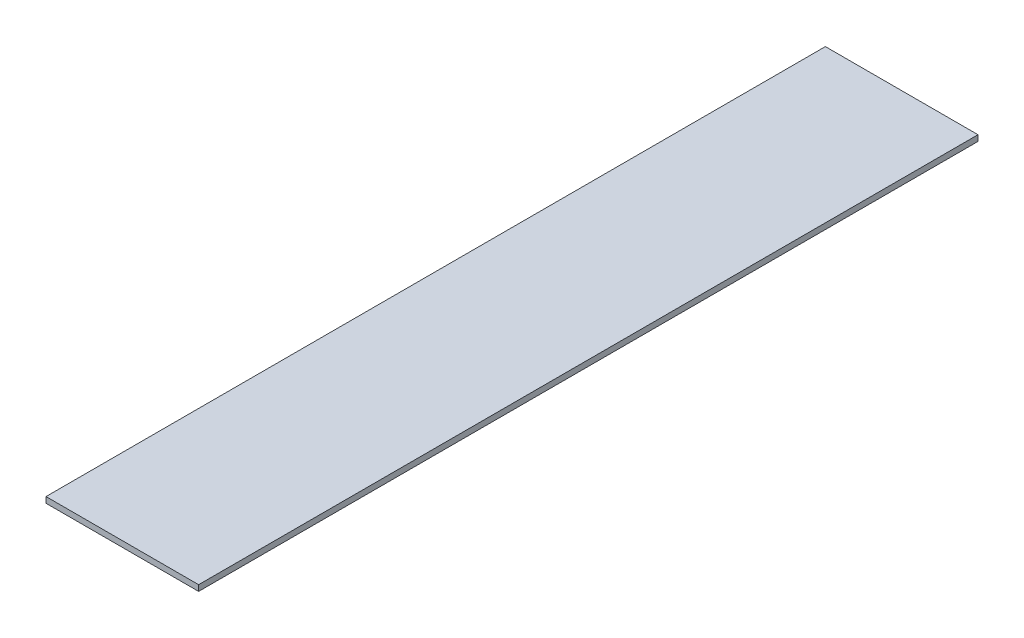
SolidWorks part; units mm, degrees
ref_plane "Front Plane" through (0, 0, 0) normal (0, 0, 1) x (1, 0, 0)
ref_plane "Top Plane" through (0, 0, 0) normal (0, 1, 0) x (1, 0, 0)
ref_plane "Right Plane" through (0, 0, 0) normal (1, 0, 0) x (0, 0, -1)
sketch "Sketch1" plane through (0, 0, 0) normal (0, 1, 0) x (1, 0, 0)
  line L1 (0, 0) -> (470, 0)
  line L2 (0, 0) -> (0, 2400)
  line L3 (0, 2400) -> (470, 2400)
  line L4 (470, 0) -> (470, 2400)
  dimension "D1" = 2400
  dimension "D2" = 470
extrude "Boss-Extrude1" add sketch "Sketch1" along normal blind 18
